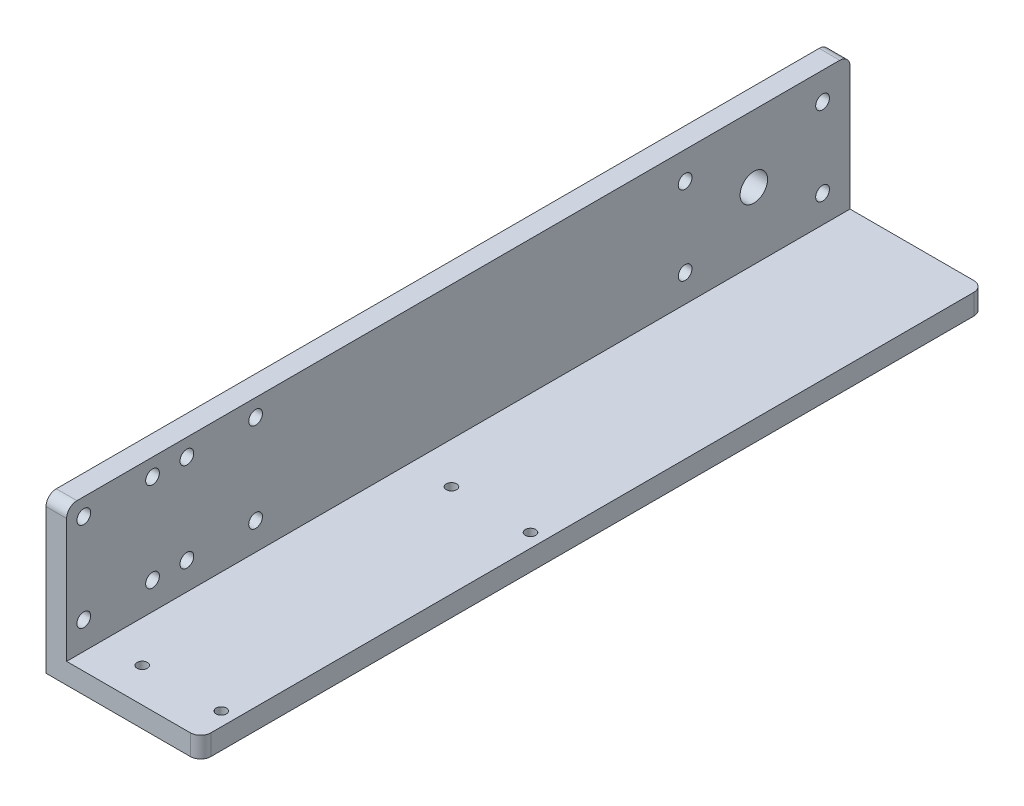
SolidWorks part; units mm, degrees
ref_plane "Front Plane" through (0, 0, 0) normal (0, 0, 1) x (1, 0, 0)
ref_plane "Top Plane" through (0, 0, 0) normal (0, 1, 0) x (1, 0, 0)
ref_plane "Right Plane" through (0, 0, 0) normal (1, 0, 0) x (0, 0, -1)
sketch "Sketch2" plane through (0, 0, 0) normal (0, 0, 1) x (1, 0, 0)
  line L0 (82.9692, 26.8) -> (82.9692, -12.2)
  line L1 (82.9692, -18.2) -> (76.9692, -18.2)
  line L4 (76.9692, -12.2) -> (76.9692, 26.8)
  line L5 (76.9692, 26.8) -> (82.9692, 26.8)
  line L6 (76.9692, -12.2) -> (76.9692, -18.2)
  line L7 (82.9692, -18.2) -> (121.9692, -18.2)
  line L8 (121.9692, -18.2) -> (121.9692, -12.2)
  line L9 (82.9692, -12.2) -> (121.9692, -12.2)
  dimension "D2" = 6
  dimension "D3" = 45
  dimension "D5" = 45
extrude "Boss-Extrude1" add sketch "Sketch2" along normal blind 228
fillet "Fillet1" radius 3 4 edges at (79.9692, 26.8, 0) (79.9692, 26.8, 228) (121.9692, -15.2, 0) (121.9692, -15.2, 228)
sketch "Sketch5" plane through (76.9692, 0, 0) normal (-1, 0, 0) x (0, 0, 1)
  line L0 (225, 26.8) -> (3, 26.8) construction
  line L1 (228, 23.8) -> (228, -18.2) construction
  line L3 (228, -12.2) -> (0, -12.2) construction
  circle A0 centre (223, 21.8) radius 2
  circle A1 centre (223, -4.2) radius 2
  circle A2 centre (203, 21.8) radius 2
  circle A3 centre (203, -4.2) radius 2
  dimension "D1" = 4
  dimension "D2" = 5
  dimension "D3" = 5
  dimension "D4" = 5
  dimension "D5" = 8
  dimension "D6" = 20
extrude "Cut-Extrude2" cut sketch "Sketch5" against normal through all
ref_plane "Plane1" through (0, 0, 198) normal (0, 0, 1) x (1, 0, 0)
mirror "Mirror1" about plane through (0, 0, 198) normal (0, 0, 1) of "Cut-Extrude2"
sketch "Sketch6" plane through (76.9692, 0, 0) normal (-1, 0, 0) x (0, 0, 1)
  line L0 (0, 23.8) -> (0, -18.2) construction
  line L1 (225, 26.8) -> (3, 26.8) construction
  line L3 (228, -12.2) -> (0, -12.2) construction
  circle A0 centre (8, 18.8) radius 2
  circle A1 centre (48, 18.8) radius 2
  circle A2 centre (8, -4.2) radius 2
  circle A3 centre (48, -4.2) radius 2
  dimension "D1" = 4
  dimension "D2" = 8
  dimension "D3" = 8
  dimension "D4" = 40
  dimension "D5" = 8
extrude "Cut-Extrude3" cut sketch "Sketch6" against normal through all
sketch "Sketch7" plane through (76.9692, 0, 0) normal (-1, 0, 0) x (0, 0, 1)
  line L0 (0, 23.8) -> (0, -18.2) construction
  line L1 (225, 26.8) -> (3, 26.8) construction
  circle A0 centre (28, 7.3) radius 4
  dimension "D1" = 8
  dimension "D2" = 28
  dimension "D3" = 19.5
extrude "Cut-Extrude4" cut sketch "Sketch7" against normal through all
ref_plane "Plane2" through (79.9692, 0, 0) normal (-1, 0, 0) x (0, 0, 1)
sketch "Sketch8" plane through (0, -12.2, 0) normal (0, 1, 0) x (1, 0, 0)
  line L0 (118.9692, -228) -> (82.9692, -228) construction
  line L1 (121.9692, -225) -> (121.9692, -3) construction
  line L2 (82.9692, -225) -> (82.9692, -3) construction
  circle A0 centre (94.9692, -218) radius 1.5
  circle A1 centre (117.9692, -218) radius 1.5
  circle A2 centre (117.9692, -128) radius 1.5
  circle A3 centre (94.9692, -128) radius 1.5
  dimension "D1" = 3
  dimension "D2" = 10
  dimension "D3" = 4
  dimension "D4" = 12
  dimension "D5" = 90
  dimension "D6" = 90
extrude "Cut-Extrude5" cut sketch "Sketch8" against normal through all
